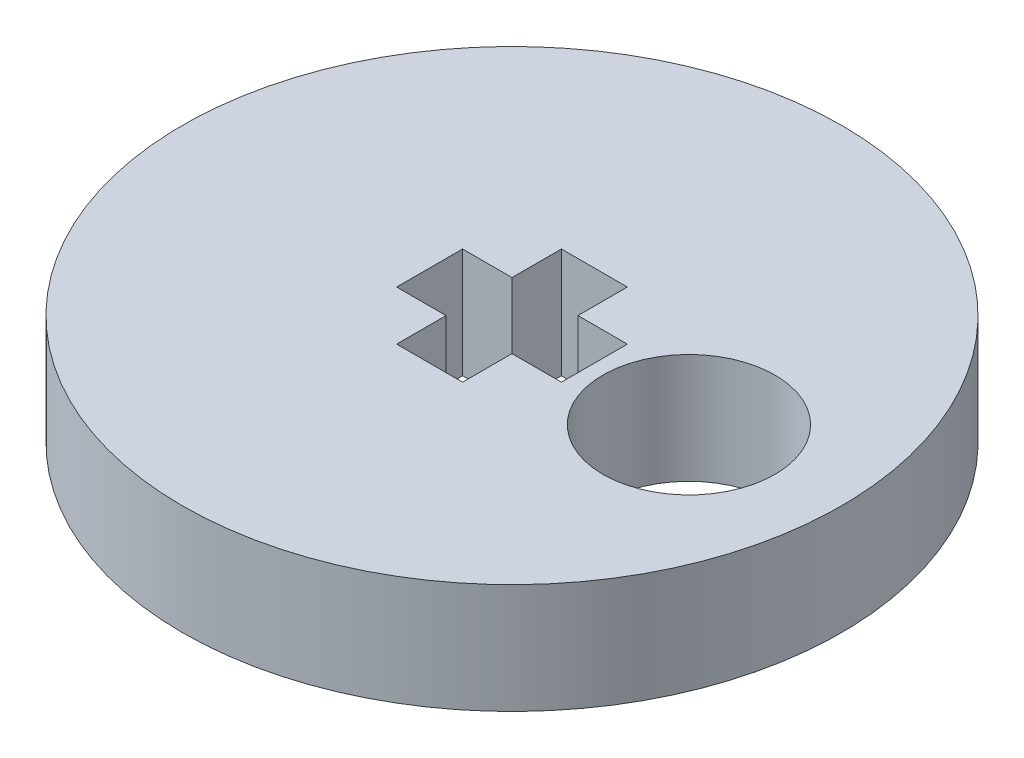
SolidWorks part; units mm, degrees
ref_plane "Front Plane" through (0, 0, 0) normal (0, 0, 1) x (1, 0, 0)
ref_plane "Top Plane" through (0, 0, 0) normal (0, 1, 0) x (1, 0, 0)
ref_plane "Right Plane" through (0, 0, 0) normal (1, 0, 0) x (0, 0, -1)
sketch "Sketch1" plane through (0, 0, 0) normal (0, 1, 0) x (1, 0, 0)
  line L6 (-2.25, 0.9) -> (-2.25, -0.9)
  line L7 (-2.25, -0.9) -> (-0.9, -0.9)
  line L8 (-0.9, -0.9) -> (-0.9, -2.25)
  line L9 (-0.9, -2.25) -> (0.9, -2.25)
  line L10 (0.9, -2.25) -> (0.9, -0.9)
  line L11 (0.9, -0.9) -> (2.25, -0.9)
  line L12 (2.25, -0.9) -> (2.25, 0.9)
  line L13 (2.25, 0.9) -> (0.9, 0.9)
  line L14 (0.9, 0.9) -> (0.9, 2.25)
  line L15 (0.9, 2.25) -> (-0.9, 2.25)
  line L16 (-0.9, 2.25) -> (-0.9, 0.9)
  line L17 (-0.9, 0.9) -> (-2.25, 0.9)
  circle A0 centre (0, 0) radius 9
  circle A1 centre (4.9973, -0.1648) radius 2.35
  circle A2 centre (0, 0) radius 2.4233 construction
  dimension "D1" = 18
  dimension "D3" = 4.7
  dimension "D2" = 4.9973
  dimension "D4" = 1.35
  dimension "D5" = 1.8
extrude "Boss-Extrude1" add sketch "Sketch1" along normal blind 3
